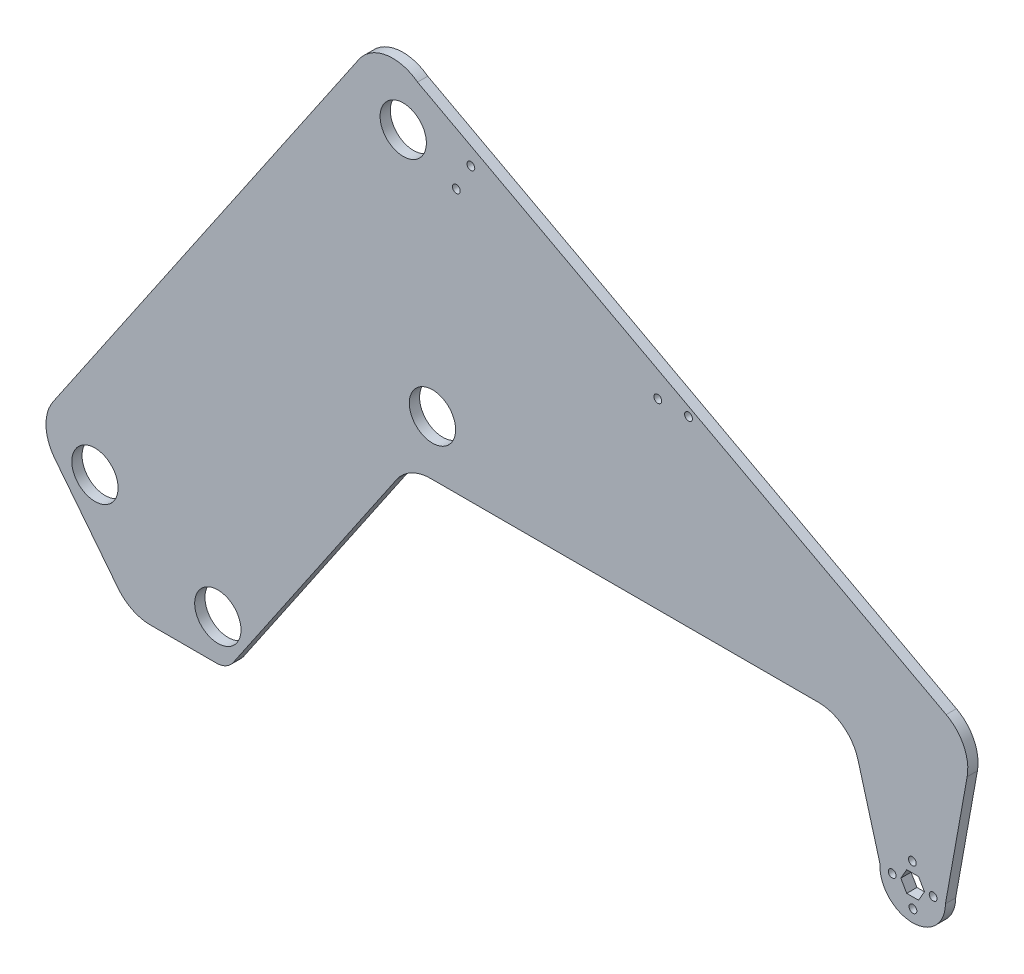
SolidWorks part; units mm, degrees
other "Markup1"
sketch "Sketch1" plane through (-441.7893, 331.8239, 6.35) normal (-0.0431, 0.0102, 0.999) x (0.9985, 0.0354, 0.0427)
sketch "Sketch2" plane through (-413.6701, 343.933, 6.35) normal (-0.0431, 0.0102, 0.999) x (0.9985, 0.0354, 0.0427)
sketch "Sketch3" plane through (-436.3774, 318.5567, 6.35) normal (-0.0431, 0.0102, 0.999) x (0.9985, 0.0354, 0.0427)
sketch "Sketch5" plane through (-436.3774, 318.5567, 6.35) normal (-0.0431, 0.0102, 0.999) x (0.9985, 0.0354, 0.0427)
sketch "Sketch7" plane through (-430.3226, 318.5567, 6.35) normal (-0.0431, 0.0102, 0.999) x (0.9985, 0.0354, 0.0427)
sketch "Sketch9" plane through (-430.3226, 318.5567, 6.35) normal (-0.0431, 0.0102, 0.999) x (0.9985, 0.0354, 0.0427)
sketch "Sketch11" plane through (-430.3226, 318.5567, 6.35) normal (-0.0431, 0.0102, 0.999) x (0.9985, 0.0354, 0.0427)
sketch "Sketch13" plane through (-430.3226, 318.5567, 6.35) normal (-0.0431, 0.0102, 0.999) x (0.9985, 0.0354, 0.0427)
sketch "Sketch15" plane through (-430.3226, 318.5567, 6.35) normal (-0.0431, 0.0102, 0.999) x (0.9985, 0.0354, 0.0427)
sketch "Sketch19" plane through (-430.3226, 318.5567, 6.35) normal (-0.0431, 0.0102, 0.999) x (0.9985, 0.0354, 0.0427)
sketch "Sketch19" plane through (-430.3226, 318.5567, 6.35) normal (-0.0431, 0.0102, 0.999) x (0.9985, 0.0354, 0.0427)
sketch "Sketch21" plane through (-430.3226, 318.5567, 6.35) normal (-0.0431, 0.0102, 0.999) x (0.9985, 0.0354, 0.0427)
sketch "Sketch23" plane through (-430.3226, 318.5567, 6.35) normal (-0.0431, 0.0102, 0.999) x (0.9985, 0.0354, 0.0427)
sketch "Sketch25" plane through (-430.3226, 318.5567, 6.35) normal (-0.0431, 0.0102, 0.999) x (0.9985, 0.0354, 0.0427)
sketch "Sketch27" plane through (-430.3226, 318.5567, 6.35) normal (-0.0431, 0.0102, 0.999) x (0.9985, 0.0354, 0.0427)
other "Markup2"
sketch "Sketch4" plane through (102.4721, 318.5567, 6.35) normal (0.9364, 0.1073, 0.3342) x (0.3416, -0.0598, -0.9379)
sketch "Sketch6" plane through (102.4721, 318.5567, 6.35) normal (0.9364, 0.1073, 0.3342) x (0.3416, -0.0598, -0.9379)
sketch "Sketch8" plane through (141.2086, 318.5567, 6.35) normal (0.9364, 0.1073, 0.3342) x (0.3416, -0.0598, -0.9379)
sketch "Sketch10" plane through (141.2086, 318.5567, 6.35) normal (0.9364, 0.1073, 0.3342) x (0.3416, -0.0598, -0.9379)
sketch "Sketch12" plane through (141.2086, 318.5567, 6.35) normal (0.9364, 0.1073, 0.3342) x (0.3416, -0.0598, -0.9379)
sketch "Sketch14" plane through (141.2086, 318.5567, 6.35) normal (0.9364, 0.1073, 0.3342) x (0.3416, -0.0598, -0.9379)
sketch "Sketch16" plane through (141.2086, 318.5567, 6.35) normal (0.9364, 0.1073, 0.3342) x (0.3416, -0.0598, -0.9379)
sketch "Sketch20" plane through (141.2086, 318.5567, 6.35) normal (0.9364, 0.1073, 0.3342) x (0.3416, -0.0598, -0.9379)
sketch "Sketch20" plane through (141.2086, 318.5567, 6.35) normal (0.9364, 0.1073, 0.3342) x (0.3416, -0.0598, -0.9379)
sketch "Sketch22" plane through (141.2086, 318.5567, 6.35) normal (0.9364, 0.1073, 0.3342) x (0.3416, -0.0598, -0.9379)
sketch "Sketch24" plane through (141.2086, 318.5567, 6.35) normal (0.9364, 0.1073, 0.3342) x (0.3416, -0.0598, -0.9379)
sketch "Sketch26" plane through (141.2086, 318.5567, 6.35) normal (0.9364, 0.1073, 0.3342) x (0.3416, -0.0598, -0.9379)
sketch "Sketch28" plane through (141.2086, 318.5567, 6.35) normal (0.9364, 0.1073, 0.3342) x (0.3416, -0.0598, -0.9379)
material "Lexan"
ref_plane "Front Plane" through (0, 0, 0) normal (0, 0, 1) x (1, 0, 0)
ref_plane "Top Plane" through (0, 0, 0) normal (0, 1, 0) x (1, 0, 0)
ref_plane "Right Plane" through (0, 0, 0) normal (1, 0, 0) x (0, 0, -1)
sketch "Model" plane through (0, 0, 0) normal (0, 0, 1) x (1, 0, 0)
  line L1 (-191.9011, 104.6502) -> (-112.96, 104.6502)
  line L3 (-314.2383, -55.3595) -> (-212.8994, 93.5413)
  line L4 (-236.3032, 307.4477) -> (-425.9209, 28.8361)
  line L5 (-424.8981, -1.1437) -> (-385.5815, -51.2028)
  line L13 (114.3386, 35.8116) -> (110.6724, 42.1616)
  line L14 (110.6724, 42.1616) -> (103.3401, 42.1616)
  line L15 (103.3401, 42.1616) -> (99.6739, 35.8116)
  line L16 (99.6739, 35.8116) -> (103.3401, 29.4616)
  line L17 (103.3401, 29.4616) -> (110.6724, 29.4616)
  line L18 (110.6724, 29.4616) -> (114.3386, 35.8116)
  line L19 (-365.606, -60.914) -> (-324.7375, -60.914)
  line L20 (-871.0211, -88.854) -> (370.1019, -88.854) construction
  line L22 (127.3262, 35.8116) -> (140.8079, 110.8095)
  line L28 (-399.9752, 2.586) -> (-323.7752, -35.514) construction
  line L29 (-323.7752, -35.514) -> (-190.7071, 138.5169) construction
  line L30 (-190.7071, 138.5169) -> (-208.8329, 283.4378) construction
  line L31 (-208.8329, 283.4378) -> (-399.9752, 2.586) construction
  line L32 (86.727, 37.0982) -> (73.1352, 86.0462)
  line L33 (48.6612, 104.6502) -> (-11.3966, 104.6502)
  line L34 (106.8234, 42.1616) -> (106.8234, 48.5116)
  line L35 (127.8091, 137.6897) -> (-86.3327, 252.4836)
  line L36 (-112.96, 104.6502) -> (-68.51, 104.6502)
  line L37 (-122.3008, 271.7648) -> (-85.2777, 251.9181)
  line L38 (-156.701, 288.2074) -> (-155.3641, 287.4328)
  line L39 (-49.867, 219.9669) -> (-44.4668, 230.0407)
  line L40 (-68.51, 104.6502) -> (-2.1388, 104.6502)
  line L41 (-122.3008, 271.7648) -> (-199.9496, 313.3896)
  line L44 (-199.9496, 313.3896) -> (-165.7592, 287.0167)
  line L45 (-155.3641, 287.4328) -> (-154.5079, 289.0299)
  arc A3 (106.824, 42.1589) -> (106.8234, 42.1616) centre (81.3892, 35.8116) ccw
  circle A9 centre (-323.7752, -35.514) radius 14.351
  circle A10 centre (-399.9752, 2.586) radius 14.351
  circle A12 centre (-190.7071, 138.5169) radius 14.351
  arc A21 (-191.9011, 104.6502) -> (-212.8994, 93.5413) centre (-191.9011, 79.2502) ccw
  circle A22 centre (-208.8329, 283.4378) radius 14.351
  circle A24 centre (107.0062, 35.8116) radius 6.35 construction
  arc A31 (-324.7375, -60.914) -> (-314.2383, -55.3595) centre (-324.7375, -48.214) ccw
  arc A44 (-236.3032, 307.4477) -> (-199.9496, 313.3896) centre (-215.305, 293.1567) cw
  arc A45 (-365.606, -60.914) -> (-385.5815, -51.2028) centre (-365.606, -35.514) cw
  arc A46 (73.1352, 86.0462) -> (48.6612, 104.6502) centre (48.6612, 79.2502) ccw
  arc A47 (140.8079, 110.8095) -> (127.8091, 137.6897) centre (115.8086, 115.3033) ccw
  arc A48 (-424.8981, -1.1437) -> (-425.9209, 28.8361) centre (-404.9226, 14.5451) cw
  circle A50 centre (-51.0071, 217.8402) radius 2.413
  circle A52 centre (-31.9571, 217.8402) radius 2.413
  circle A53 centre (-166.8993, 284.89) radius 2.413
  circle A55 centre (-175.8997, 268.1002) radius 2.413
  circle A56 centre (-171.3995, 276.4951) radius 2.413 [skipped]
  circle A57 centre (-41.4821, 217.8402) radius 2.413 [skipped]
  arc A58 (86.727, 37.0982) -> (127.3262, 35.8116) centre (107.0062, 35.8116) ccw
  circle A65 centre (106.8234, 48.5116) radius 2.413
  circle A66 centre (119.7062, 35.9944) radius 2.413
  circle A67 centre (107.1891, 23.1116) radius 2.413
  circle A68 centre (94.3062, 35.6287) radius 2.413
  ellipse E0 centre (-551.1692, 173.9527) end of major axis (-591.2054, 216.0961) minor radius 17.278
  point P31 (-177.5612, 330.9695)
  point P43 (-377.9543, -60.914)
  point P60 (-205.3388, 104.6502)
  point P64 (-436.3774, 13.472)
  point P75 (107.0062, 35.8116)
  point P83 (107.0062, 35.8116)
  dimension "D3" = 38.1
  dimension "D5" = 76.2
  dimension "D6" = 40.64
  dimension "D7" = 6.35
  dimension "D8" = 28.702
  dimension "D11" = 139.7
  dimension "D12" = 27.94
  dimension "D21" = 124.238
  dimension "D13" = 12.7
  dimension "D16" = 355.6
  dimension "D23" = 242.9699
  dimension "D24" = 76.2
  dimension "D14" = 50.8
  dimension "D20" = 254
  dimension "D29" = 25.4
  dimension "D31" = 25.4
  dimension "D32" = 25.4
  dimension "D33" = 25.4
  dimension "D34" = 176.784
  dimension "D35" = 19.05
  dimension "D37" = 3
  dimension "D36" = 4.826
  dimension "D41" = 4.826
  dimension "D43" = 19.05
  dimension "D19" = 4.826
  dimension "D9" = 19.05
  dimension "D10" = 146.05
  dimension "D15" = 33.8667
  dimension "D17" = 339.725
  dimension "D18" = 219.075
  dimension "D22" = 25.4
  dimension "D27" = 53.2168
  dimension "D39" = 11.43
  dimension ".3" = 11.43
  dimension "D40" = 43.18
  dimension "D42" = 3
extrude "Boss-Extrude1" add sketch "Model" along normal blind 6.35
